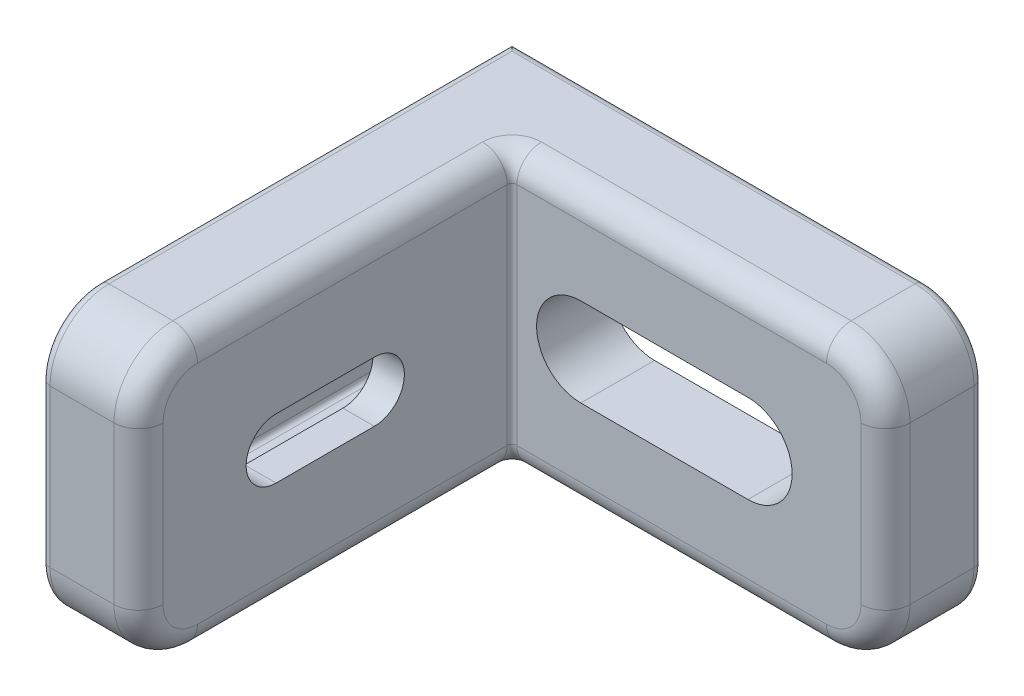
SolidWorks part; units mm, degrees
ref_plane "Front Plane" through (0, 0, 0) normal (0, 0, 1) x (1, 0, 0)
ref_plane "Top Plane" through (0, 0, 0) normal (0, 1, 0) x (1, 0, 0)
ref_plane "Right Plane" through (0, 0, 0) normal (1, 0, 0) x (0, 0, -1)
ref_plane "Plane1" through (0, 28, 0) normal (0, 1, 0) x (1, 0, 0)
sketch "Sketch1" plane through (0, 28, 0) normal (0, 1, 0) x (1, 0, 0)
  line L0 (0, -48) -> (48, -48)
  line L1 (48, -48) -> (48, 0)
  line L2 (48, 0) -> (0, 0)
  line L3 (0, 0) -> (0, -48)
extrude "Boss-Extrude1" add sketch "Sketch1" against normal blind 28
sketch "Sketch2" plane through (0, 28, 0) normal (0, 1, 0) x (-1, 0, 0)
  line L0 (-48, 10) -> (-10, 10)
  line L1 (-10, 10) -> (-10, 48)
  line L2 (-10, 48) -> (-48, 48)
  line L3 (-48, 48) -> (-48, 10)
extrude "Cut-Extrude1" cut sketch "Sketch2" against normal through all
sketch "Sketch3" plane through (0, 0, 0) normal (0, 0, -1) x (-1, 0, 0)
  line L0 (0, 22.2) -> (-41, 22.2)
  line L1 (-41, 22.2) -> (-41, 5.8)
  line L2 (-41, 5.8) -> (0, 5.8)
  line L3 (0, 5.8) -> (0, 22.2)
extrude "Cut-Extrude2" cut sketch "Sketch3" against normal blind 2.5
sketch "Sketch4" plane through (0, 0, 2.5) normal (0, 0, -1) x (-1, 0, 0)
  line L0 (-6.8, 8.65) -> (-3.2, 8.65)
  line L1 (-3.2, 8.65) -> (-3.2, 19.35)
  line L2 (-3.2, 19.35) -> (-6.8, 19.35)
  line L3 (-6.8, 19.35) -> (-6.8, 8.65)
extrude "Cut-Extrude3" cut sketch "Sketch4" against normal blind 38.5
sketch "Sketch5" plane through (0, 0, 0) normal (-1, 0, 0) x (0, 0, 1)
  line L0 (2.5, 17.05) -> (2.5, 10.95)
  line L1 (2.5, 10.95) -> (34, 10.95)
  line L2 (34, 17.05) -> (2.5, 17.05)
  arc A0 (34, 10.95) -> (34, 17.05) centre (34, 14) ccw
extrude "Cut-Extrude4" cut sketch "Sketch5" against normal up to next
sketch "Sketch6" plane through (6.8, 0, 0) normal (-1, 0, 0) x (0, 0, 1)
  line L0 (34, 17.05) -> (24, 17.05)
  line L1 (24, 10.95) -> (34, 10.95)
  arc A0 (34, 10.95) -> (34, 17.05) centre (34, 14) ccw
  arc A1 (24, 17.05) -> (24, 10.95) centre (24, 14) ccw
extrude "Cut-Extrude5" cut sketch "Sketch6" against normal through all
sketch "Sketch7" plane through (0, 0, 2.5) normal (0, 0, -1) x (-1, 0, 0)
  line L0 (-17, 18.5) -> (-34, 18.5)
  line L1 (-34, 9.5) -> (-17, 9.5)
  arc A0 (-34, 18.5) -> (-34, 9.5) centre (-34, 14) ccw
  arc A1 (-17, 9.5) -> (-17, 18.5) centre (-17, 14) ccw
extrude "Cut-Extrude6" cut sketch "Sketch7" against normal through all
fillet "Fillet1" radius 6 4 edges at (5, 0, 48) (5, 28, 48) (48, 0, 5) (48, 28, 5)
fillet "Fillet2" radius 0.5 4 edges at (3.2, 8.65, 21.75) (6.8, 19.35, 21.75) (10, 14, 10) (6.8, 8.65, 21.75)
fillet "Fillet3" radius 1 10 edges at (21, 0, 0) (46.2426, 1.7574, 0) (21, 28, 0) (48, 14, 0) (46.2426, 26.2426, 0) (0, 0, 21) (0, 1.7574, 46.2426) (0, 14, 48) (0, 28, 21) (0, 26.2426, 46.2426)
fillet "Fillet4" radius 2.5 12 edges at (26.25, 28, 10) (10.1464, 28, 10.1464) (46.2426, 26.2426, 10) (10, 28, 26.25) (48, 14, 10) (10, 26.2426, 46.2426) (46.2426, 1.7574, 10) (10, 14, 48) (26.25, 0, 10) (10, 1.7574, 46.2426) (10.1464, 0, 10.1464) (10, 0, 26.25)
